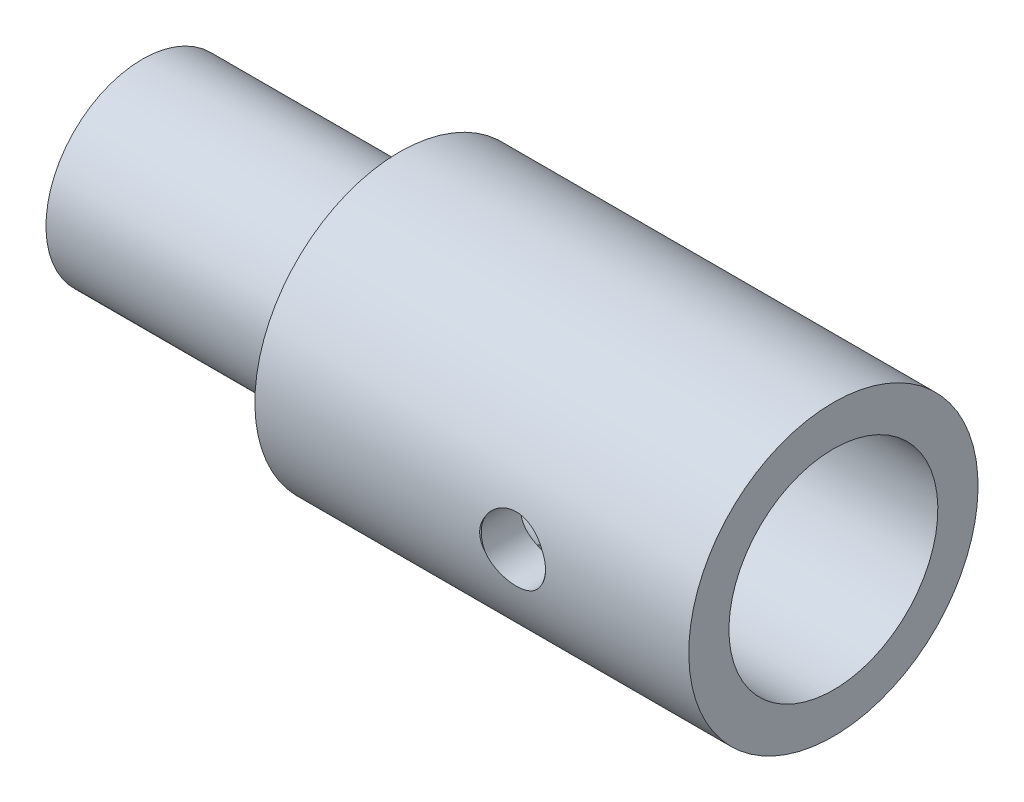
SolidWorks part; units mm, degrees
material "Ceramic Porcelain"
ref_plane "Front Plane" through (0, 0, 0) normal (0, 0, 1) x (1, 0, 0)
ref_plane "Top Plane" through (0, 0, 0) normal (0, 1, 0) x (1, 0, 0)
ref_plane "Right Plane" through (0, 0, 0) normal (1, 0, 0) x (0, 0, -1)
sketch "Sketch1" plane through (0, 0, 0) normal (0, 0, 1) x (1, 0, 0)
  line L0 (0, -1.9719) -> (-11.9286, -1.9719) construction
  line L1 (9.5497, 1.2781) -> (9.5497, 2.5281)
  line L2 (9.5497, 1.2781) -> (1.5497, 1.2781)
  line L3 (1.5497, 1.2781) -> (1.5497, 1.0281)
  line L4 (1.5497, 1.0281) -> (-2.4503, 1.0281)
  line L6 (-2.4503, 2.5281) -> (9.5497, 2.5281)
  line L7 (-2.4503, 1.0281) -> (-2.4503, -0.4719)
  line L8 (-2.4503, -0.4719) -> (-11.9503, -0.4719)
  line L9 (-11.9503, -0.4719) -> (-11.9503, 1.0281)
  line L10 (-2.4503, -0.4719) -> (-2.4503, 1.0281)
  line L12 (-2.4503, 2.5281) -> (-3.9503, 2.5281)
  line L13 (-3.9503, 2.5281) -> (-3.9503, 1.0281)
  line L14 (-3.9503, 1.0281) -> (-11.9503, 1.0281)
  dimension "D1" = 0.25
  dimension "D2" = 1.5
  dimension "D3" = 3
  dimension "D4" = 8
  dimension "D5" = 4
  dimension "D6" = 3
  dimension "D7" = 1.5
  dimension "D8" = 8
  dimension "D9" = 1.5
revolve "Revolve1" add sketch "Sketch1" angle 360 about L0
hole_wizard "Ø2.0 (2) Diameter Hole1" positions "3DSketch1" profile "Sketch4" hole size "Ø2.0" standard "ANSI Metric" end condition through all
sketch3d "3DSketch1"
  point P0 (4.0682, -1.9657, 4.5)
sketch "Sketch4" plane through (4.0682, -1.9657, 4.5) normal (1, 0, 0) x (0, -1, 0.0014)
  line L0 (0, 0) -> (0, 9.0061)
  line L1 (0, 9.0061) -> (1, 9.0061)
  line L2 (1, 9.0061) -> (1, 0.025)
  line L3 (1, 0.025) -> (1.025, 0)
  line L5 (1.025, 0) -> (0, 0)
  line L6 (-1, 0.025) -> (-1.025, 0) construction
  line L11 (0, -6.35) -> (0, 107.95) construction
  dimension "Thru Hole Dia." = 2
  dimension "Thru Hole Depth" = 9.0061
  dimension "Near C'Sink Dia." = 2.05
  dimension "Near C'Sink Angle" = 90
